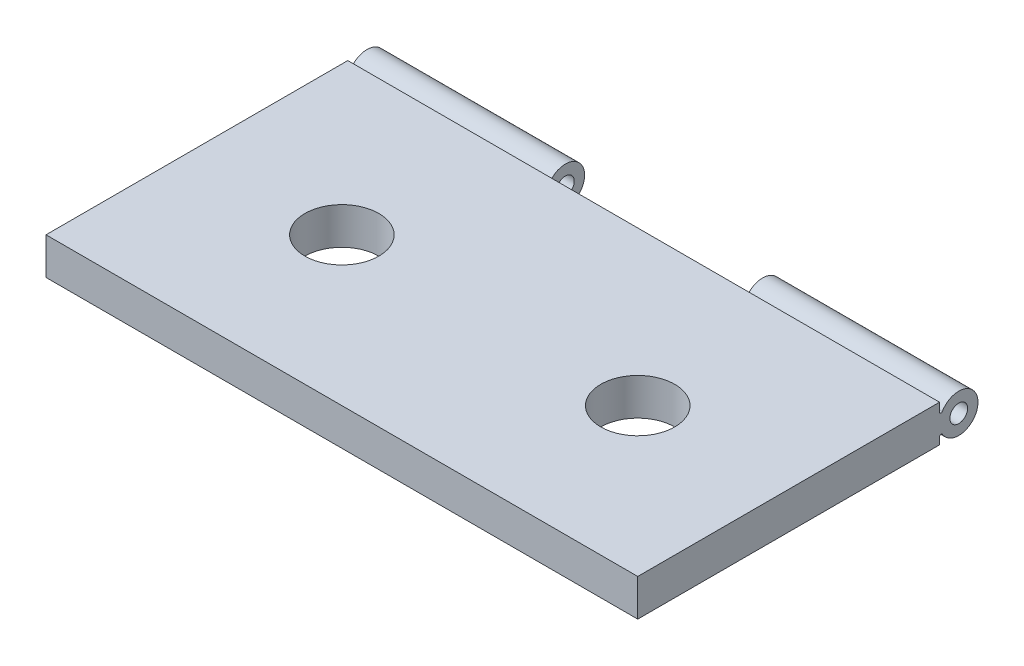
SolidWorks part; units mm, degrees
ref_plane "Alzado" through (0, 0, 0) normal (0, 0, 1) x (1, 0, 0)
ref_plane "Planta" through (0, 0, 0) normal (0, 1, 0) x (1, 0, 0)
ref_plane "Vista lateral" through (0, 0, 0) normal (1, 0, 0) x (0, 0, -1)
sketch "Croquis3" plane through (0, 0, 0) normal (0, 1, 0) x (1, 0, 0)
  line L1 (25.4, -12.7) -> (-25.4, -12.7)
  line L2 (25.4, -12.7) -> (25.4, 12.7)
  line L3 (25.4, 12.7) -> (-25.4, 12.7)
  line L4 (-25.4, -12.7) -> (-25.4, 12.7)
  line L5 (25.4, -12.7) -> (-25.4, 12.7) construction
  line L6 (25.4, 12.7) -> (-25.4, -12.7) construction
  circle A0 centre (-12.7, 0) radius 3.175
  circle A1 centre (12.7, 0) radius 3.175
  point P0 (0, 0)
  dimension "D5" = 6.35
  dimension "D6" = 6.35
  dimension "D1" = 25.4
  dimension "D2" = 50.8
  dimension "D3" = 12.7
  dimension "D4" = 12.7
extrude "Saliente-Extruir1" add sketch "Croquis3" along normal blind 3.175
ref_plane "Plano1" through (0, 0, 0) normal (-1, 0, 0) x (0, 0, 1)
sketch "Croquis4" plane through (-25.4, 0, 0) normal (-1, 0, 0) x (0, 0, 1)
  line L0 (13.97, 0) -> (-13.97, 0) construction
  line L1 (12.7, 3.175) -> (13.208, 3.175)
  line L2 (12.7, 3.175) -> (12.7, 0)
  line L3 (12.7, 0) -> (13.208, 0)
  line L4 (13.208, 3.175) -> (13.208, 2.2784)
  line L5 (13.208, 0.9103) -> (13.208, 0)
  circle A0 centre (14.9761, 1.5944) radius 0.762
  arc A1 (13.208, 2.2784) -> (13.4522, 2.2296) centre (13.335, 2.2784) ccw
  arc A2 (13.4522, 0.9592) -> (13.208, 0.9103) centre (13.335, 0.9103) ccw
  arc A3 (13.4522, 0.9592) -> (13.4522, 2.2296) centre (14.9761, 1.5944) ccw
  dimension "D2" = 0.254
  dimension "D3" = 0.254
  dimension "D4" = 3.302
  dimension "D5" = 1.524
  dimension "D1" = 0.508
extrude "Saliente-Extruir2" [suppressed] add sketch "Croquis4" along normal mid plane 16.9333
sketch "Croquis6" plane through (0, 0, 0) normal (-1, 0, 0) x (0, 0, 1)
  line L0 (16.0596, 0) -> (-16.0596, 0) construction
  line L1 (-12.7, 3.175) -> (-13.208, 3.175)
  line L2 (-12.7, 3.175) -> (-12.7, 0)
  line L3 (-12.7, 0) -> (-13.208, 0)
  line L4 (-13.208, 3.175) -> (-13.208, 2.4375)
  line L5 (-13.208, 0.6059) -> (-13.208, 0)
  arc A0 (-13.208, 0.6059) -> (-13.4439, 0.6713) centre (-13.335, 0.6059) ccw
  arc A1 (-13.4439, 2.3721) -> (-13.4439, 0.6713) centre (-14.859, 1.5217) ccw
  arc A2 (-13.4439, 2.3721) -> (-13.208, 2.4375) centre (-13.335, 2.4375) ccw
  circle A3 centre (-14.859, 1.5217) radius 0.762
  dimension "D2" = 0.254
  dimension "D3" = 0.254
  dimension "D4" = 3.302
  dimension "D5" = 1.524
  dimension "D1" = 0.508
extrude "Saliente-Extruir3" add sketch "Croquis6" along normal mid plane 16.9333
sketch "Croquis7" plane through (25.4, 0, 0) normal (1, 0, 0) x (0, 0, -1)
  line L0 (12.7, 3.175) -> (13.208, 3.175) construction
  line L1 (13.208, 3.175) -> (13.208, 2.4375) construction
  line L2 (13.208, 0.6059) -> (13.208, 0) construction
  line L3 (13.208, 0) -> (12.7, 0) construction
  line L4 (12.7, 3.175) -> (12.7, 0) construction
  line L5 (12.7, 3.175) -> (13.208, 3.175)
  line L6 (13.208, 3.175) -> (13.208, 2.4375)
  line L7 (13.208, 0.6059) -> (13.208, 0)
  line L8 (13.208, 0) -> (12.7, 0)
  line L9 (12.7, 3.175) -> (12.7, 0)
  arc A0 (13.208, 2.4375) -> (13.4439, 2.3721) centre (13.335, 2.4375) ccw construction
  arc A1 (13.4439, 0.6713) -> (13.4439, 2.3721) centre (14.859, 1.5217) ccw construction
  circle A2 centre (14.859, 1.5217) radius 0.762 construction
  arc A3 (13.4439, 0.6713) -> (13.208, 0.6059) centre (13.335, 0.6059) ccw construction
  arc A4 (13.208, 2.4375) -> (13.4439, 2.3721) centre (13.335, 2.4375) ccw
  arc A5 (13.4439, 0.6713) -> (13.4439, 2.3721) centre (14.859, 1.5217) ccw
  circle A6 centre (14.859, 1.5217) radius 0.762
  arc A7 (13.4439, 0.6713) -> (13.208, 0.6059) centre (13.335, 0.6059) ccw
extrude "Saliente-Extruir4" add sketch "Croquis7" against normal offset from surface (50.8 mm away) 50.8 up to face at (25.4, 1.5875, 0)
sketch "Croquis8" plane through (0, 3.175, 0) normal (0, 1, 0) x (1, 0, 0)
  line L0 (-25.4, 13.208) -> (25.4, 13.208) construction
  line L1 (-8.3706, 13.208) -> (8.5627, 13.208)
  line L2 (-8.3706, 13.208) -> (-8.3706, 16.51)
  line L3 (-8.3706, 16.51) -> (8.5627, 16.51)
  line L4 (8.5627, 13.208) -> (8.5627, 16.51)
  line L5 (25.4, 16.51) -> (-25.4, 16.51) construction
  line L6 (0, 12.3317) -> (0, -12.3317) construction
  line L7 (0, 0) -> (0.0961, 16.51) construction
  dimension "D1" = 16.9333
extrude "Cortar-Extruir2" cut sketch "Croquis8" against normal blind 25.4
